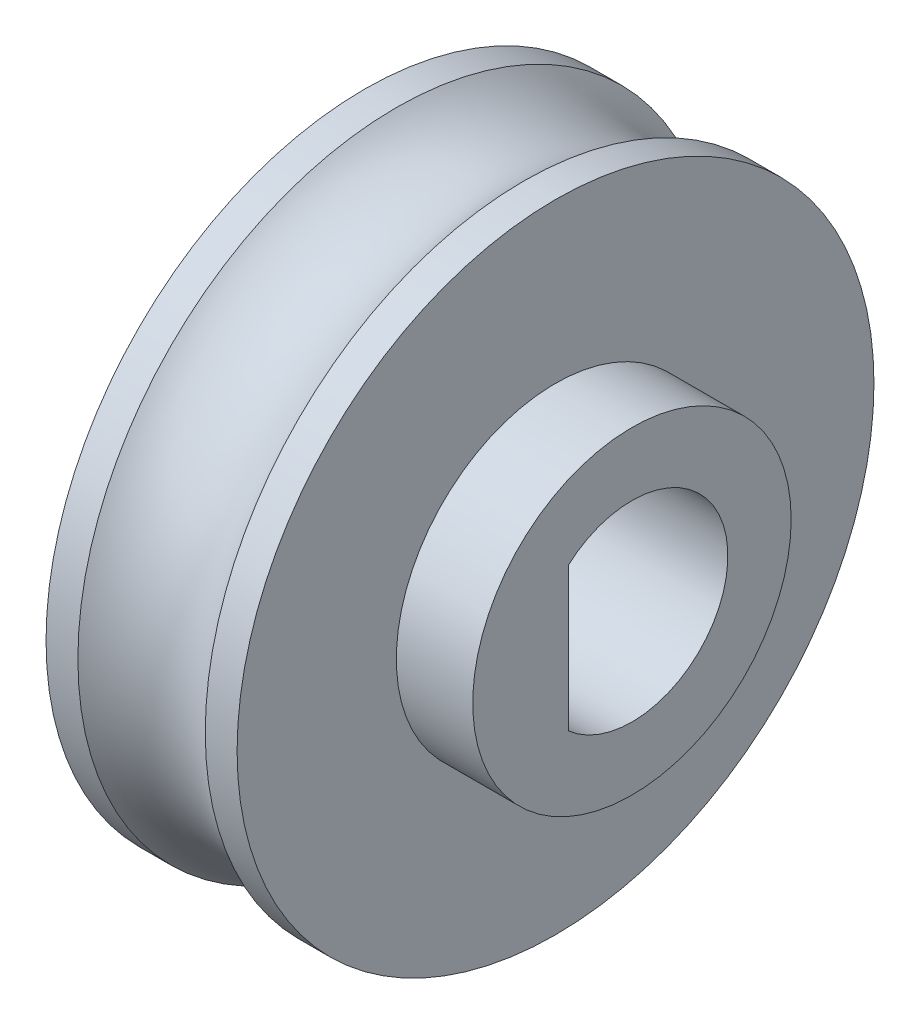
SolidWorks part; units mm, degrees
ref_plane "Front Plane" through (0, 0, 0) normal (0, 0, 1) x (1, 0, 0)
ref_plane "Top Plane" through (0, 0, 0) normal (0, 1, 0) x (1, 0, 0)
ref_plane "Right Plane" through (0, 0, 0) normal (1, 0, 0) x (0, 0, -1)
sketch "Sketch3" plane through (0, 0, 0) normal (0, 0, 1) x (1, 0, 0)
  line L0 (0, 0) -> (8.6831, 0) construction
  line L1 (0, 0) -> (0, 6.0025) construction
  line L2 (-1.5, 0) -> (1.5, 0)
  line L3 (1.5, 0) -> (1.5, 5)
  line L4 (1.5, 5) -> (1, 5)
  line L5 (-1.5, 0) -> (-1.5, 5)
  line L6 (-1.5, 5) -> (-1, 5)
  arc A0 (1, 5) -> (-1, 5) centre (0, 6.118) cw
  dimension "D2" = 1.5
  dimension "D1" = 5
  dimension "D3" = 0.5
  dimension "D4" = 1.5
revolve "Revolve1" add sketch "Sketch3" angle 360 about L0
sketch "Sketch7" plane through (1.5, 0, 0) normal (1, 0, 0) x (0, 0, -1)
  circle A0 centre (0, 0) radius 2.5
  dimension "D1" = 5
extrude "Boss-Extrude1" add sketch "Sketch7" along normal blind 1.2
sketch "Sketch5" plane through (1.5, 0, 0) normal (1, 0, 0) x (0, 0, -1)
  line L0 (-1, 1.126) -> (-1, -1.126)
  arc A0 (-1, -1.126) -> (-1, 1.126) centre (0, 0) ccw
  dimension "D1" = 1
extrude "Cut-Extrude1" cut sketch "Sketch5" against normal through all both and the other way through all
sketch "Sketch9" plane through (-1.5, 0, 0) normal (-1, 0, 0) x (0, 0, 1)
  circle A0 centre (0, 0) radius 3.5
  dimension "D1" = 7
extrude "Cut-Extrude2" cut sketch "Sketch9" against normal blind 1
